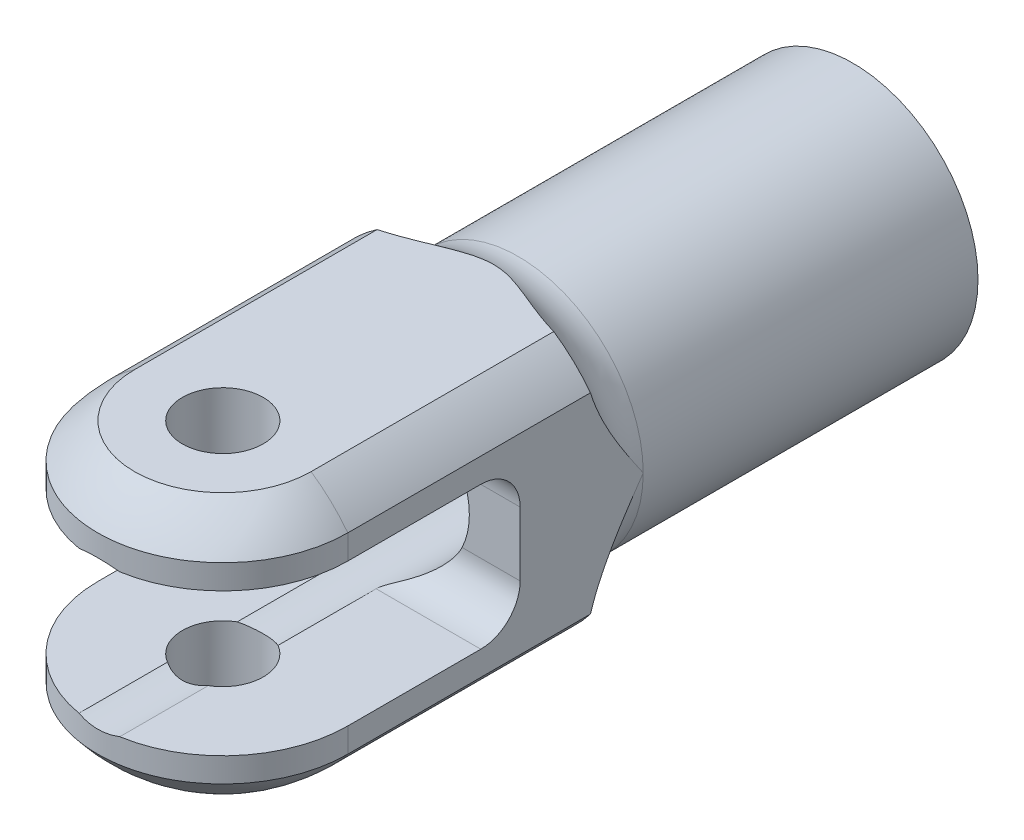
SolidWorks part; units mm, degrees
material "7075-T6 (SN)"
ref_plane "Front Plane" through (0, 0, 0) normal (0, 0, 1) x (1, 0, 0)
ref_plane "Top Plane" through (0, 0, 0) normal (0, 1, 0) x (1, 0, 0)
ref_plane "Right Plane" through (0, 0, 0) normal (1, 0, 0) x (0, 0, -1)
sketch "Sketch1" plane through (0, 0, 0) normal (0, 0, 1) x (1, 0, 0)
  circle A0 centre (0, 0) radius 12.7
  dimension "D1" = 25.4
extrude "Extrude1" add sketch "Sketch1" along normal blind 90
sketch "Sketch11" plane through (0, 0, 0) normal (0, 0, -1) x (-1, 0, 0)
  circle A0 centre (0, 0) radius 18.9
  dimension "D1" = 37.8
extrude "Boss-Extrude1" add sketch "Sketch11" against normal blind 50 from offset 40 offset against normal yes
fillet "Fillet1" radius 6 1 edges at (-12.7, 0, 40)
sketch "Sketch2" plane through (0, 0, 0) normal (0, 1, 0) x (1, 0, 0)
  line L0 (12.7, 0) -> (-12.7, 0) construction
  line L1 (-12.7, -90) -> (12.7, -90) construction
  line L2 (12.7, 0) -> (-12.7, 0)
  line L4 (0, 0) -> (0, -90) construction
  line L5 (-12.7, -90) -> (12.7, -90) construction
  line L6 (-12.7, 0) -> (-12.7, -64)
  line L7 (12.7, 0) -> (12.7, -64)
  line L8 (12.7, -34) -> (12.7, 0) construction
  arc A0 (-12.7, -64) -> (12.7, -64) centre (0, -64) ccw
  circle A1 centre (0, -64) radius 4.1021
  dimension "D2" = 8.2042
  dimension "D1" = 64
extrude "Extrude3" cut sketch "Sketch2" against normal through all and the other way through all flip side to cut
sketch "Sketch3" plane through (0, 0, 0) normal (1, 0, 0) x (0, 0, -1)
  line L0 (-76.7, 18.9) -> (-76.7, -18.9) construction
  line L1 (-106.9, 7.25) -> (-50.5, 7.25)
  line L2 (-106.9, 7.25) -> (-106.9, -7.25)
  line L3 (-106.9, -7.25) -> (-50.5, -7.25)
  line L4 (-46.5, 3.25) -> (-46.5, -3.25)
  line L5 (-106.9, 7.25) -> (-46.5, -7.25) construction
  line L6 (-106.9, -7.25) -> (-46.5, 7.25) construction
  line L7 (-68.1021, 12.7) -> (0, 12.7) construction
  line L9 (0, -12.7) -> (-59.8979, -12.7) construction
  arc A0 (-46.5, 3.25) -> (-50.5, 7.25) centre (-50.5, 3.25) ccw
  arc A1 (-50.5, -7.25) -> (-46.5, -3.25) centre (-50.5, -3.25) ccw
  point P0 (-76.7, 0)
  dimension "D3" = 4
  dimension "D1" = 14.5
  dimension "D2" = 46.5
extrude "Extrude4" cut sketch "Sketch3" against normal through all and the other way through all
sketch "Sketch4" plane through (0, 0, 46.5) normal (0, 0, 1) x (1, 0, 0)
  point P0 (0, 0)
sketch "Sketch7" plane through (0, 0, 0) normal (0, 0, 1) x (1, 0, 0)
  circle A4 centre (0, 0) radius 7.54
  dimension "D1" = 15.08
extrude "Extrude5" cut sketch "Sketch7" along normal through all from offset 8
sketch "Sketch8" plane through (0, 0, 46.5) normal (0, 0, 1) x (1, 0, 0)
  circle A0 centre (0, 0) radius 5
  dimension "D1" = 10
extrude "Cut-Extrude1" cut sketch "Sketch8" against normal through all
sketch3d "3DSketch2"
  line L0 (0, 7.25, 64) -> (0, -7.25, 64) construction
  line L1 (0, 7.25, 64) -> (0, 18.9, 64) construction
  line L2 (0, -18.9, 64) -> (0, -7.25, 64) construction
  line L3 (0, 0, 0) -> (0, 0, 46.5) construction
  point P10 (0, 0, 64)
sketch "Sketch12" plane through (0, 0, 0) normal (1, 0, 0) x (0, 0, -1)
  line L0 (0, 0) -> (-95.9642, 0) construction
  line L1 (-50.5, 7.25) -> (-64, 7.25) construction
  line L2 (-85.1523, 13.25) -> (-25.6127, 13.25)
  line L3 (-85.1523, 13.25) -> (-85.1523, 28.0608)
  line L4 (-85.1523, 28.0608) -> (-25.6127, 28.0608)
  line L5 (-25.6127, 13.25) -> (-25.6127, 28.0608)
  line L6 (-25.6127, -13.25) -> (-25.6127, -28.0608)
  line L7 (-85.1523, -28.0608) -> (-25.6127, -28.0608)
  line L8 (-85.1523, -13.25) -> (-85.1523, -28.0608)
  line L9 (-85.1523, -13.25) -> (-25.6127, -13.25)
  dimension "D1" = 6
extrude "Cut-Extrude2" cut sketch "Sketch12" against normal through all and the other way through all
sketch "Sketch13" plane through (0, 0, 0) normal (0, 0, 1) x (1, 0, 0)
  circle A0 centre (0, 0) radius 16
  dimension "D1" = 32
extrude "Cut-Extrude3" cut sketch "Sketch13" along normal through all flip side to cut
sketch "Sketch14" plane through (0, 0, 0) normal (1, 0, 0) x (0, 0, -1)
  line L0 (-64, 16) -> (-64, 21.2218)
  line L1 (-64, 21.2218) -> (-91.2178, 21.2218)
  line L2 (-91.2178, 21.2218) -> (-91.2178, 0)
  line L3 (-91.2178, 0) -> (-80, 0)
  line L4 (-64, 0) -> (-94.2928, 0) construction
  arc A0 (-80, 0) -> (-64, 16) centre (-64, 0) cw
  dimension "D1" = 16
revolve "Cut-Revolve1" cut sketch "Sketch14" angle 360 about L4
